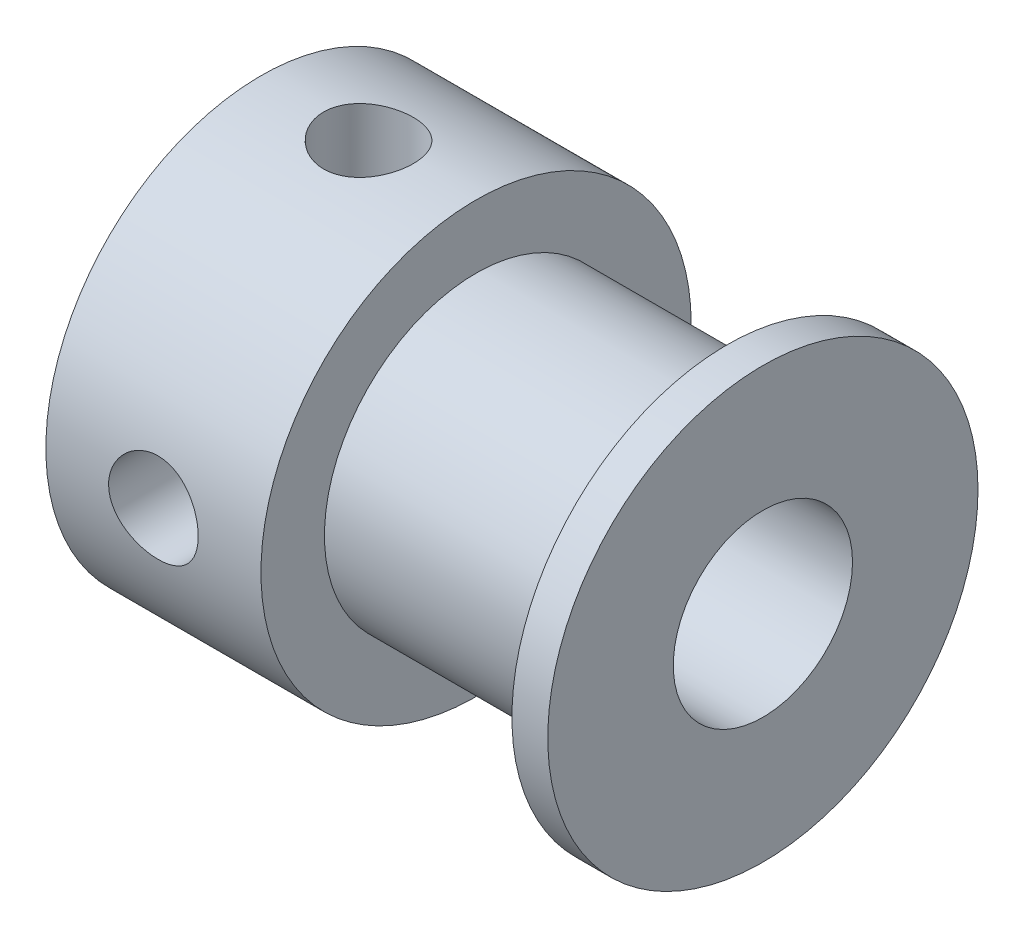
SolidWorks part; units mm, degrees
material "6061-T6 (SS)"
ref_plane "Front Plane" through (0, 0, 0) normal (0, 0, 1) x (1, 0, 0)
ref_plane "Top Plane" through (0, 0, 0) normal (0, 1, 0) x (1, 0, 0)
ref_plane "Right Plane" through (0, 0, 0) normal (1, 0, 0) x (0, 0, -1)
sketch "Sketch1" plane through (0, 0, 0) normal (0, 0, 1) x (1, 0, 0)
  line L0 (0, 2.5) -> (0, 6)
  line L1 (0, 6) -> (6, 6)
  line L2 (6, 6) -> (6, 4.2291)
  line L3 (6, 4.2291) -> (13, 4.2291)
  line L4 (13, 4.2291) -> (13, 6)
  line L5 (13, 6) -> (14, 6)
  line L6 (14, 6) -> (14, 2.5)
  line L7 (14, 2.5) -> (0, 2.5)
  line L8 (0, 0) -> (-7.6744, 0) construction
  dimension "D1" = 5
  dimension "D2" = 12
  dimension "D3" = 8.4582
  dimension "D4" = 6
  dimension "D5" = 14
  dimension "D6" = 1
revolve "Revolve1" add sketch "Sketch1" angle 360 about L8
hole_wizard "M3x0.5 Tapped Hole1" positions "Sketch3" profile "Sketch2" tap size "M3x0.5" standard "ANSI Metric"
sketch "Sketch3" plane through (0, 0, 0) normal (0, 1, 0) x (1, 0, 0)
  line L0 (0, 0) -> (6, 0) construction
  line L1 (6, -4.2291) -> (6, 4.2291) construction
  point P8 (3, 0)
sketch "Sketch2" plane through (3, 0, 0) normal (1, 0, 0) x (0, 0, -1)
  line L0 (0, 0) -> (0, 6)
  line L1 (0, 6) -> (1.25, 6)
  line L2 (1.25, 6) -> (1.25, 0)
  line L5 (1.25, 0) -> (0, 0)
  line L11 (0, -6.35) -> (0, 107.95) construction
  dimension "Thread Major Dia." = 2.5
  dimension "Thru Tap Drill Depth" = 6
hole_wizard "M3x0.5 Tapped Hole2" positions "Sketch5" profile "Sketch4" tap size "M3x0.5" standard "ANSI Metric"
sketch "Sketch5" plane through (0, 0, 0) normal (0, 0, 1) x (1, 0, 0)
  line L0 (0, 0) -> (6, 0) construction
  line L1 (6, -4.2291) -> (6, 4.2291) construction
  point P7 (3, 0)
sketch "Sketch4" plane through (3, 0, 0) normal (1, 0, 0) x (0, 1, 0)
  line L0 (0, 0) -> (0, 6)
  line L1 (0, 6) -> (1.25, 6)
  line L2 (1.25, 6) -> (1.25, 0)
  line L5 (1.25, 0) -> (0, 0)
  line L11 (0, -6.35) -> (0, 107.95) construction
  dimension "Thread Major Dia." = 2.5
  dimension "Thru Tap Drill Depth" = 6
